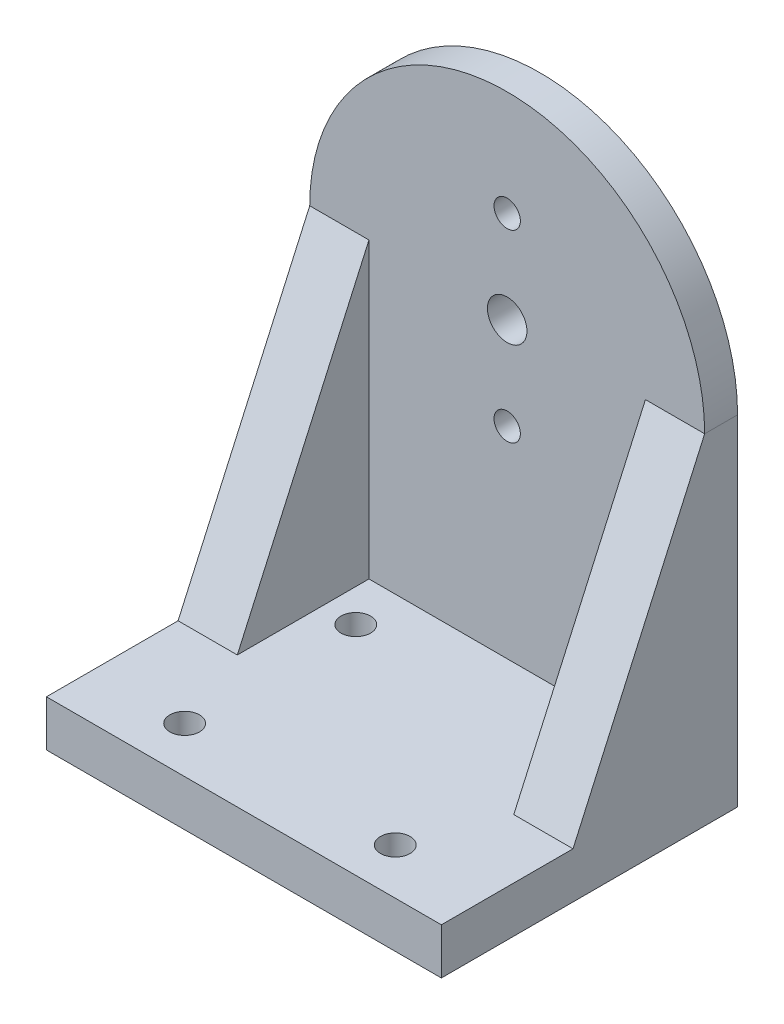
SolidWorks part; units mm, degrees
ref_plane "Front Plane" through (0, 0, 0) normal (0, 0, 1) x (1, 0, 0)
ref_plane "Top Plane" through (0, 0, 0) normal (0, 1, 0) x (1, 0, 0)
ref_plane "Right Plane" through (0, 0, 0) normal (1, 0, 0) x (0, 0, -1)
sketch "Sketch1" plane through (0, 0, 0) normal (0, 0, 1) x (1, 0, 0)
  line L2 (-30, 26.6) -> (-30, -25)
  line L3 (-30, -25) -> (30, -25)
  line L4 (30, 26.6) -> (30, -25)
  arc A0 (-30, 26.6) -> (30, 26.6) centre (0, 26.6) cw
  circle A1 centre (0, 26.6) radius 3
  circle A2 centre (0, 40.6) radius 2
  circle A3 centre (0, 12.6) radius 2
  point P0 (0, 0)
  dimension "D3" = 30
  dimension "D4" = 6
  dimension "D5" = 4
  dimension "D6" = 4
  dimension "D7" = 14
  dimension "D8" = 14
  dimension "D1" = 60
  dimension "D2" = 51.6
extrude "Boss-Extrude1" add sketch "Sketch1" along normal blind 5
sketch "Sketch2" plane through (0, 0, 5) normal (0, 0, 1) x (1, 0, 0)
  line L0 (30, -25) -> (30, 26.6) construction
  line L1 (-30, -25) -> (30, -25)
  line L2 (-30, -25) -> (-30, -18)
  line L3 (-30, -18) -> (30, -18)
  line L4 (30, -25) -> (30, -18)
  dimension "D1" = 7
extrude "Boss-Extrude2" add sketch "Sketch2" along normal blind 40
sketch "Sketch3" plane through (-30, 0, 0) normal (-1, 0, 0) x (0, 0, 1)
  line L0 (5, 26.6) -> (25, -18)
  line L1 (45, -18) -> (5, -18) construction
  line L2 (25, -18) -> (5, -18)
  line L3 (5, -18) -> (5, 26.6)
  line L4 (45, -18) -> (45, -25) construction
  dimension "D1" = 44.6
  dimension "D2" = 20
extrude "Boss-Extrude3" add sketch "Sketch3" against normal blind 9
mirror "Mirror1" about plane through (0, 0, 0) normal (1, 0, 0) of "Boss-Extrude3"
sketch "Sketch4" plane through (0, -18, 0) normal (0, 1, 0) x (1, 0, 0)
  line L0 (-21, -5) -> (-21, -25) construction
  line L2 (21, -5) -> (-21, -5) construction
  circle A0 centre (16, -38) radius 2.25
  circle A1 centre (-16, -38) radius 2.25
  circle A2 centre (-16, -12) radius 2.25
  circle A3 centre (16, -12) radius 2.25
  dimension "D1" = 32
  dimension "D2" = 26
  dimension "D3" = 4.5
  dimension "D4" = 26
  dimension "D5" = 32
  dimension "D6" = 5
  dimension "D7" = 7
  dimension "D8" = 7
extrude "Cut-Extrude1" cut sketch "Sketch4" against normal through all
